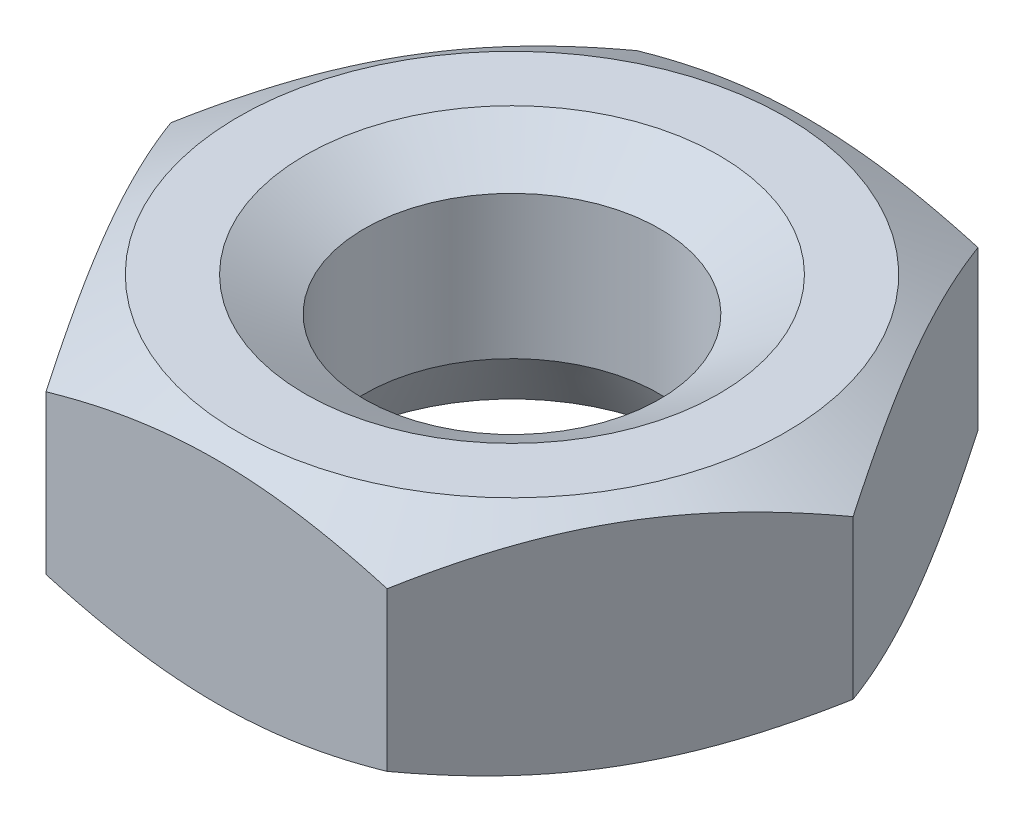
SolidWorks part; units mm, degrees
material "Простая углеродистая сталь"
ref_plane "Спереди" through (0, 0, 0) normal (0, 0, 1) x (1, 0, 0)
ref_plane "Сверху" through (0, 0, 0) normal (0, 1, 0) x (1, 0, 0)
ref_plane "Справа" through (0, 0, 0) normal (1, 0, 0) x (0, 0, -1)
sketch "Эскиз1" plane through (0, 0, 0) normal (0, 1, 0) x (1, 0, 0)
  line L1 (-5.7735, 0) -> (-2.8868, -5)
  line L2 (-2.8868, -5) -> (2.8868, -5)
  line L3 (2.8868, -5) -> (5.7735, 0)
  line L4 (5.7735, 0) -> (2.8868, 5)
  line L5 (2.8868, 5) -> (-2.8868, 5)
  line L6 (-2.8868, 5) -> (-5.7735, 0)
  circle A0 centre (0, 0) radius 5 construction
  circle A1 centre (0, 0) radius 2.5
  dimension "D1" = 5
  dimension "D2" = 10
extrude "Бобышка-Вытянуть1" add sketch "Эскиз1" along normal blind 4
chamfer "Фаска1" distance 1 angle 30 2 edges at (0, 4, 2.5) (0, 0, 2.5)
sketch "Эскиз2" plane through (0, 0, 0) normal (1, 0, 0) x (0, 0, -1)
  line L0 (0, 2) -> (5.4308, 2) construction
  line L1 (0, 4) -> (0, 0) construction
  line L5 (0, 0) -> (5, 0) construction
  line L10 (4.6282, 0) -> (6.6282, 0)
  line L11 (6.6282, 0) -> (6.6282, 1.1547)
  line L12 (4.6282, 0) -> (6.6282, 1.1547)
  line L13 (4.6282, 4) -> (6.6282, 2.8453)
  line L14 (6.6282, 4) -> (6.6282, 2.8453)
  line L15 (4.6282, 4) -> (6.6282, 4)
  line L16 (0, 0) -> (0, 4) construction
  dimension "D1" = 2
  dimension "D2" = 30
revolve "Вырез-Повернуть1" cut sketch "Эскиз2" angle 360 about L16
